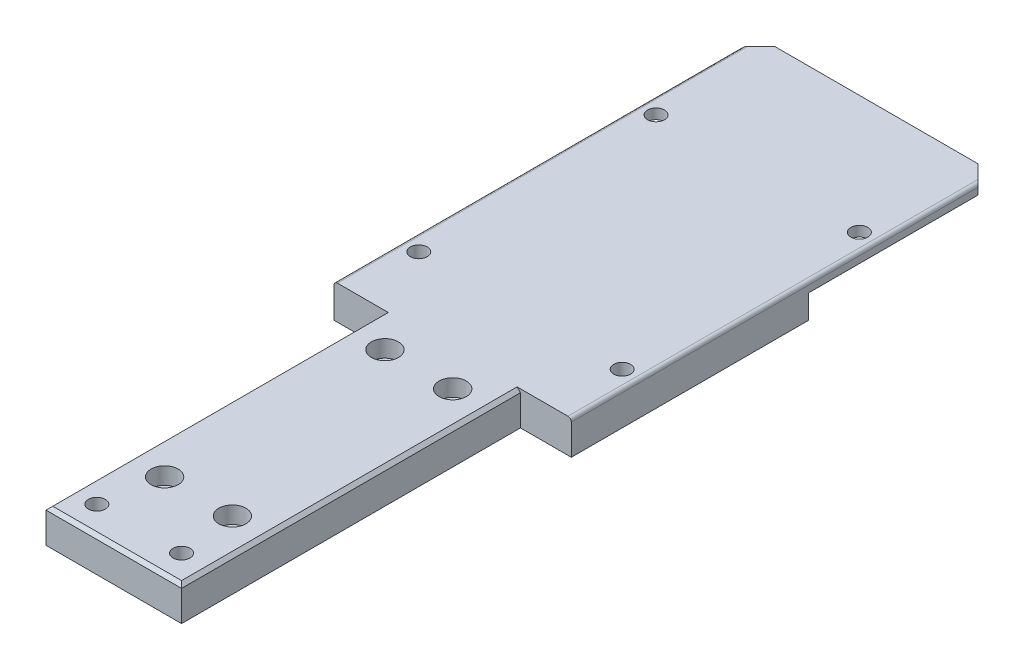
SolidWorks part; units mm, degrees
ref_plane "Front Plane" through (0, 0, 0) normal (0, 0, 1) x (1, 0, 0)
ref_plane "Top Plane" through (0, 0, 0) normal (0, 1, 0) x (1, 0, 0)
ref_plane "Right Plane" through (0, 0, 0) normal (1, 0, 0) x (0, 0, -1)
sketch "Sketch2" plane through (0, 0, 0) normal (0, 1, 0) x (1, 0, 0)
  line L0 (0, 0) -> (40, 0)
  line L1 (40, 0) -> (40, 100)
  line L2 (40, 100) -> (55, 100)
  line L3 (55, 100) -> (55, 220)
  line L4 (55, 220) -> (50, 225)
  line L5 (50, 225) -> (-10, 225)
  line L6 (-10, 225) -> (-15, 220)
  line L7 (-15, 220) -> (-15, 100)
  line L8 (-15, 100) -> (0, 100)
  line L9 (0, 100) -> (0, 0)
  point P3 (20, 225)
  point P12 (20, 0)
  dimension "D1" = 40
  dimension "D2" = 15
  dimension "D3" = 15
  dimension "D4" = 125
  dimension "D5" = 120
  dimension "D6" = 100
extrude "Boss-Extrude1" add sketch "Sketch2" along normal blind 10
sketch "Sketch3" plane through (0, 0, 0) normal (0, -1, 0) x (1, 0, 0)
  line L0 (-15, -220) -> (-10, -225)
  line L1 (-10, -225) -> (50, -225)
  line L2 (50, -225) -> (55, -220)
  line L3 (55, -220) -> (55, -170)
  line L4 (55, -100) -> (55, -220) construction
  line L5 (55, -170) -> (-15, -170)
  line L6 (-15, -220) -> (-15, -100) construction
  line L7 (-15, -170) -> (-15, -220)
  dimension "D1" = 50
extrude "Cut-Extrude1" cut sketch "Sketch3" against normal blind 7
sketch "Sketch4" plane through (0, 10, 0) normal (0, 1, 0) x (1, 0, 0)
  line L0 (0, 0) -> (40, 0) construction
  line L1 (0, 100) -> (0, 0) construction
  line L2 (40, 0) -> (40, 100) construction
  circle A0 centre (10, 25) radius 4
  circle A1 centre (30, 25) radius 4
  circle A2 centre (10, 90) radius 4
  circle A3 centre (30, 90) radius 4
  dimension "D1" = 8
  dimension "D2" = 25
  dimension "D3" = 10
  dimension "D4" = 10
  dimension "D5" = 65
extrude "Cut-Extrude2" cut sketch "Sketch4" against normal blind 5
sketch "Sketch5" plane through (0, 5, 0) normal (0, 1, 0) x (1, 0, 0)
  circle A0 centre (30, 90) radius 2.5
  circle A1 centre (10, 90) radius 2.5
  circle A2 centre (10, 25) radius 2.5
  circle A3 centre (30, 25) radius 2.5
  dimension "D1" = 5
extrude "Cut-Extrude3" cut sketch "Sketch5" against normal through all
sketch "Sketch6" plane through (0, 10, 0) normal (0, 1, 0) x (1, 0, 0)
  line L0 (50, 225) -> (-10, 225) construction
  line L1 (55, 100) -> (55, 220) construction
  line L2 (-15, 220) -> (-15, 100) construction
  line L3 (40, 100) -> (55, 100) construction
  circle A0 centre (50, 190) radius 2.5
  circle A1 centre (-10, 190) radius 2.5
  circle A2 centre (-10, 120) radius 2.5
  circle A3 centre (50, 120) radius 2.5
  dimension "D1" = 5
  dimension "D2" = 5
  dimension "D3" = 5
  dimension "D4" = 5
  dimension "D5" = 35
  dimension "D6" = 5
  dimension "D7" = 5
  dimension "D8" = 20
extrude "Cut-Extrude4" cut sketch "Sketch6" against normal through all
sketch "Sketch7" plane through (0, 10, 0) normal (0, 1, 0) x (1, 0, 0)
  line L0 (0, 0) -> (40, 0) construction
  line L1 (40, 0) -> (40, 100) construction
  circle A0 centre (32, 8) radius 2.5
  circle A1 centre (7, 8.0104) radius 2.5
  point P4 (30, 8.7056)
  point P5 (6.8729, 8.7048)
  dimension "D1" = 5
  dimension "D2" = 5
  dimension "D3" = 25
  dimension "D4" = 8
  dimension "D5" = 8
extrude "Cut-Extrude5" cut sketch "Sketch7" against normal through all
chamfer "Chamfer1" distance 1 angle 45 3 edges at (0, 10, -50) (40, 10, -50) (20, 10, 0)
fillet "Fillet1" radius 1 2 edges at (55, 10, -160) (-15, 10, -160)
